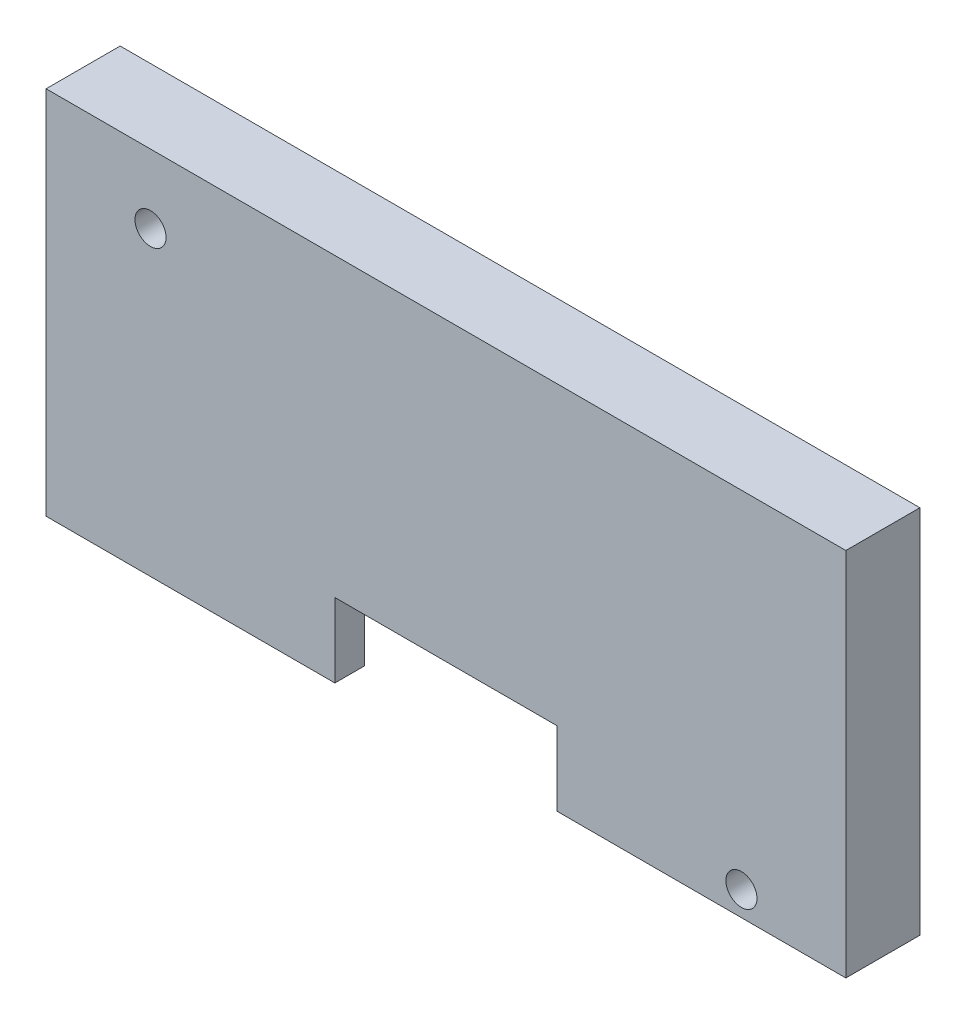
SolidWorks part; units mm, degrees
ref_plane "前基準面" through (0, 0, 0) normal (0, 0, 1) x (1, 0, 0)
ref_plane "上基準面" through (0, 0, 0) normal (0, 1, 0) x (1, 0, 0)
ref_plane "右基準面" through (0, 0, 0) normal (1, 0, 0) x (0, 0, -1)
sketch "草圖1" plane through (0, 0, 0) normal (0, 0, 1) x (1, 0, 0)
  line L0 (10.0368, -17.5816) -> (10.0368, 39.2742) construction
  line L1 (-16.9632, 7.4184) -> (37.0368, 7.4184)
  line L2 (-16.9632, 7.4184) -> (-16.9632, -17.5816)
  line L3 (-16.9632, -17.5816) -> (37.0368, -17.5816)
  line L4 (37.0368, 7.4184) -> (37.0368, -17.5816)
  line L5 (-16.9632, -5.0816) -> (46.383, -5.0816) construction
  dimension "D1" = 54
  dimension "D2" = 25
extrude "填料-伸長1" add sketch "草圖1" along normal blind 5 contours L1 L4 L3 L2
sketch "草圖2" plane through (0, 0, 0) normal (0, 0, 1) x (1, 0, 0)
  line L0 (-16.9632, -17.5816) -> (37.0368, -17.5816) construction
  line L1 (-14.9632, 4.4184) -> (35.0368, 4.4184)
  line L2 (-14.9632, 4.4184) -> (-14.9632, -17.5816)
  line L3 (-14.9632, -17.5816) -> (35.0368, -17.5816)
  line L4 (35.0368, 4.4184) -> (35.0368, -17.5816)
  line L5 (10.0368, -17.5816) -> (10.0368, 15.8472) construction
  line L6 (-14.9632, -6.5816) -> (35.0368, -6.5816) construction
  line L8 (-16.9632, 7.4184) -> (-16.9632, -17.5816) construction
  dimension "D1" = 50
  dimension "D2" = 22
  dimension "D3" = 2
extrude "除料-伸長1" cut sketch "草圖2" along normal blind 3
sketch "草圖3" plane through (0, 0, 0) normal (0, 0, 1) x (1, 0, 0)
  line L0 (35.0368, -17.5816) -> (35.0368, 4.4184) construction
  line L1 (-14.9632, -17.5816) -> (35.0368, -17.5816) construction
  line L2 (-14.9632, 4.4184) -> (-14.9632, -17.5816) construction
  line L3 (35.0368, 4.4184) -> (-14.9632, 4.4184) construction
  circle A0 centre (29.9868, -15.9316) radius 1.05
  circle A1 centre (-9.9132, 2.7684) radius 1.05
  dimension "D1" = 2.1
  dimension "D2" = 2.1
  dimension "D4" = 0.6
  dimension "D5" = 4
  dimension "D6" = 0.6
  dimension "D3" = 4
extrude "除料-伸長2" cut sketch "草圖3" along normal blind 17 contours A1 | A0
sketch "草圖4" plane through (0, 0, 0) normal (0, 0, 1) x (1, 0, 0)
  line L0 (10.0368, -17.5816) -> (10.0368, 4.4184) construction
  line L1 (-14.9632, -17.5816) -> (35.0368, -17.5816) construction
  line L2 (35.0368, 4.4184) -> (-14.9632, 4.4184) construction
  line L4 (17.5368, -12.5816) -> (2.5368, -12.5816)
  line L5 (17.5368, -12.5816) -> (17.5368, -17.5816)
  line L6 (17.5368, -17.5816) -> (2.5368, -17.5816)
  line L7 (2.5368, -12.5816) -> (2.5368, -17.5816)
  dimension "D1" = 15
  dimension "D2" = 7.5
  dimension "D3" = 5
extrude "除料-伸長3" cut sketch "草圖4" along normal blind 18
